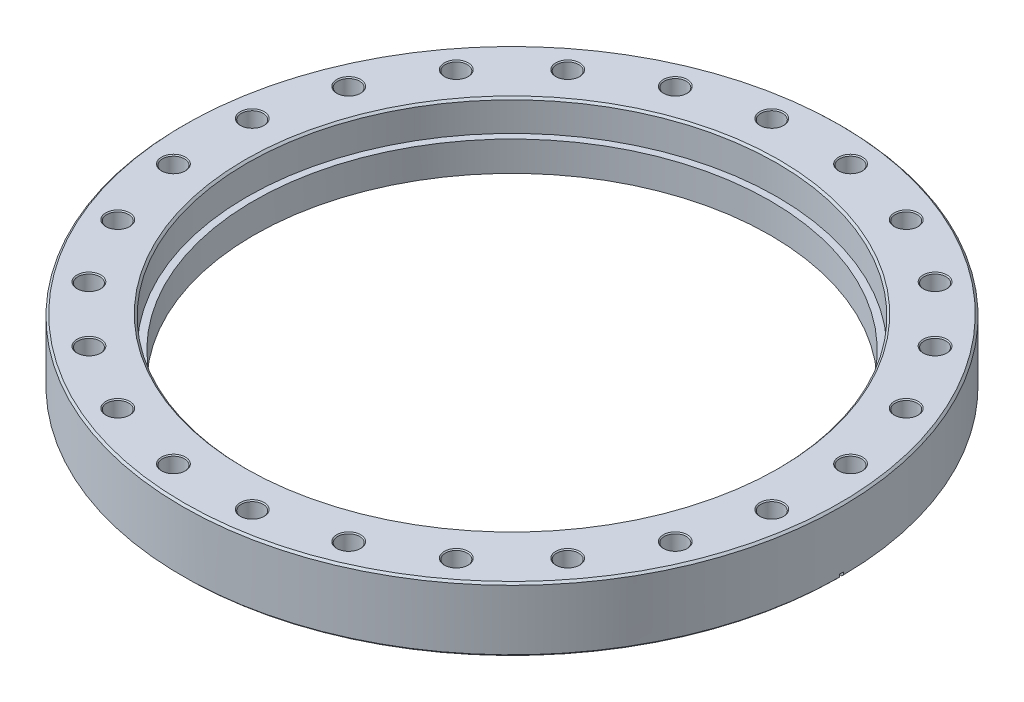
SolidWorks part; units mm, degrees
ref_plane "Front Plane" through (0, 0, 0) normal (0, 0, 1) x (1, 0, 0)
ref_plane "Top Plane" through (0, 0, 0) normal (0, 1, 0) x (1, 0, 0)
ref_plane "Right Plane" through (0, 0, 0) normal (1, 0, 0) x (0, 0, -1)
sketch "Sketch1" plane through (0, 0, 0) normal (0, 1, 0) x (1, 0, 0)
  circle A0 centre (0, 0) radius 126.619
  circle A1 centre (0, 0) radius 99.2124
  dimension "D1" = 253.238
  dimension "D2" = 198.4248
extrude "Boss-Extrude1" add sketch "Sketch1" along normal blind 24.638
sketch "Sketch2" plane through (0, 24.638, 0) normal (0, -1, 0) x (-1, 0, 0)
  circle A0 centre (0, 0) radius 101.854
  dimension "D1" = 203.708
extrude "Cut-Extrude1" cut sketch "Sketch2" along normal blind 11.938
chamfer "Chamfer1" distance 0.762 angle 45 3 edges at (0, 0, 126.619) (0, 24.638, 126.619) (0, 24.638, -101.854)
sketch "Sketch4" plane through (0, 0, 0) normal (0, 0, 1) x (1, 0, 0)
  line L0 (-111.125, 0) -> (-111.125, 1.6256)
  line L1 (-111.125, 1.6256) -> (-108.458, 0.6604)
  line L2 (-108.458, 0.6604) -> (-108.458, 1.27)
  line L3 (-108.458, 1.27) -> (0, 1.27)
  line L5 (0, 1.27) -> (0, 0)
  line L6 (0, 0) -> (-111.125, 0)
  dimension "D2" = 111.125
  dimension "D3" = 108.458
  dimension "D4" = 1.27
  dimension "D5" = 1.6256
  dimension "D6" = 0.6096
revolve "Cut-Revolve1" cut sketch "Sketch4" angle 360 about axis through (0, 24.638, 0) along (0, -1, 0)
sketch "Sketch3" plane through (0, 24.638, 0) normal (0, 1, 0) x (1, 0, 0)
  line L0 (0, 0) -> (-15.1313, 114.9338) construction
  line L1 (0, 0) -> (0, 125.857) construction
  circle A0 centre (-15.1313, 114.9338) radius 4.2164
  circle A1 centre (0, 0) radius 125.857 construction
  dimension "D2" = 8.4328
  dimension "D1" = 7.5
  dimension "D3" = 115.9256
extrude "Cut-Extrude2" cut sketch "Sketch3" against normal through all
chamfer "Chamfer2" distance 0.381 angle 45 2 edges at (-15.1313, 24.638, -110.7174) (-15.1313, 0, -110.7174)
pattern_circular "CirPattern1" count 24 every 15 about axis through (0, 0, 0) along (0, 1, 0) of "Cut-Extrude2", "Chamfer2"
sketch "Sketch5" plane through (0, 0, 0) normal (0, 0, 1) x (1, 0, 0)
  line L0 (-109.6245, 0.8878) -> (-126.619, 1.7784)
  line L1 (-126.619, 1.7784) -> (-126.619, -4.8574)
  line L2 (-126.619, -4.8574) -> (-109.6245, -4.8574)
  line L3 (0, -4.8574) -> (-109.6245, 0.8878) construction
  line L4 (-109.6245, 0.8878) -> (-109.6245, -4.8574)
  line L5 (-109.6245, -4.8574) -> (0, -4.8574) construction
  line L6 (109.6245, 0.8878) -> (109.6245, -4.8574)
  line L7 (126.619, -4.8574) -> (109.6245, -4.8574)
  line L8 (0, -4.8574) -> (0, 0) construction
  line L9 (126.619, 1.7784) -> (126.619, -4.8574)
  line L10 (109.6245, 0.8878) -> (126.619, 1.7784)
  dimension "D1" = 4.8574
  dimension "D3" = 3
extrude "Cut-Extrude3" cut sketch "Sketch5" against normal mid plane 1.5875
